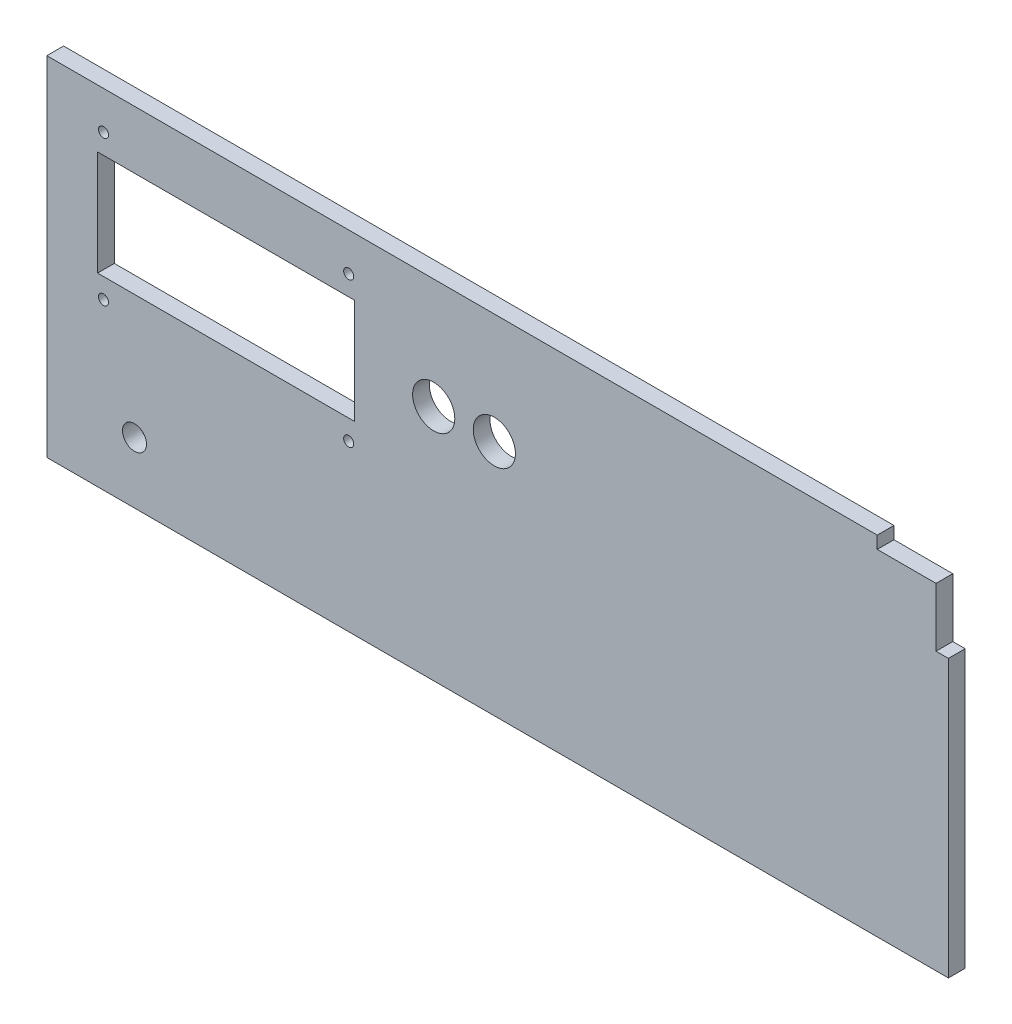
SolidWorks part; units mm, degrees
ref_plane "Front Plane" through (0, 0, 0) normal (0, 0, 1) x (1, 0, 0)
ref_plane "Top Plane" through (0, 0, 0) normal (0, 1, 0) x (1, 0, 0)
ref_plane "Right Plane" through (0, 0, 0) normal (1, 0, 0) x (0, 0, -1)
sketch "Sketch1" plane through (0, 0, 0) normal (0, 0, 1) x (1, 0, 0)
  line L1 (0, 0) -> (342, 0)
  line L2 (0, 0) -> (0, 132)
  line L15 (116.75, 90.1) -> (146.75, 90.1) construction
  line L16 (146.75, 90.1) -> (169.75, 90.1) construction
  line L17 (19.25, 70.2) -> (19.25, 23.2) construction
  line L18 (19.25, 23.2) -> (33.25, 23.2) construction
  line L19 (19.25, 70.2) -> (116.75, 70.2)
  line L20 (19.25, 70.2) -> (19.25, 110)
  line L21 (19.25, 110) -> (116.75, 110)
  line L22 (116.75, 70.2) -> (116.75, 110)
  line L23 (19.25, 70.2) -> (116.75, 110) construction
  line L24 (19.25, 110) -> (116.75, 70.2) construction
  line L25 (315, 132) -> (315, 127.3)
  line L26 (315, 127.3) -> (337.3, 127.3)
  line L27 (337.3, 127.3) -> (337.3, 105)
  line L28 (337.3, 105) -> (342, 105)
  line L29 (342, 0) -> (342, 105)
  line L30 (0, 132) -> (315, 132)
  circle A0 centre (114.5, 117.6) radius 1.9
  circle A1 centre (114.5, 62.6) radius 1.9
  circle A2 centre (21.5, 62.6) radius 1.9
  circle A3 centre (21.5, 117.6) radius 1.9
  circle A4 centre (146.75, 90.1) radius 8
  circle A5 centre (169.75, 90.1) radius 8
  circle A6 centre (33.25, 23.2) radius 4.55
  point P1 (339.65, 105)
  point P22 (68, 90.1)
  dimension "D5" = 3.8
  dimension "D6" = 3.8
  dimension "D7" = 3.8
  dimension "D8" = 3.8
  dimension "D16" = 30
  dimension "D17" = 16
  dimension "D19" = 16
  dimension "D22" = 9.1
  dimension "D1" = 132
  dimension "D3" = 27.5
  dimension "D4" = 46.5
  dimension "D9" = 68
  dimension "D10" = 4.7
  dimension "D11" = 97.5
  dimension "D12" = 39.8
  dimension "D13" = 27.5
  dimension "D14" = 46.5
  dimension "D18" = 23
  dimension "D20" = 47
  dimension "D21" = 14
  dimension "D23" = 4.7
  dimension "D24" = 27
  dimension "D25" = 27
  dimension "D26" = 342
  dimension "D27" = 22
extrude "Boss-Extrude1" add sketch "Sketch1" along normal blind 6.35
